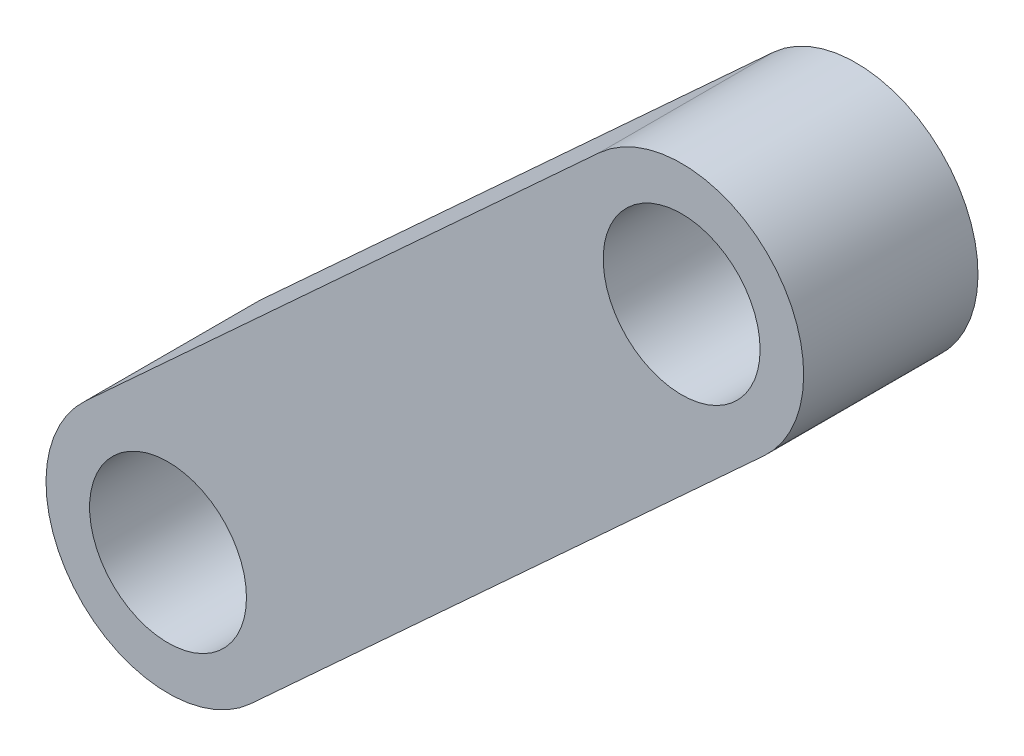
SolidWorks part; units mm, degrees
ref_plane "Front Plane" through (0, 0, 0) normal (0, 0, 1) x (1, 0, 0)
ref_plane "Top Plane" through (0, 0, 0) normal (0, 1, 0) x (1, 0, 0)
ref_plane "Right Plane" through (0, 0, 0) normal (1, 0, 0) x (0, 0, -1)
sketch "Sketch1" plane through (0, 0, 0) normal (0, 0, 1) x (1, 0, 0)
  line L0 (0, 0) -> (294.6187, 270.5547) construction
  line L1 (-47.3471, 51.5583) -> (247.2716, 322.1129)
  line L2 (47.3471, -51.5583) -> (341.9658, 218.9964)
  arc A0 (-47.3471, 51.5583) -> (47.3471, -51.5583) centre (0, 0) ccw
  arc A1 (341.9658, 218.9964) -> (247.2716, 322.1129) centre (294.6187, 270.5547) ccw
  circle A2 centre (0, 0) radius 45
  circle A3 centre (294.6187, 270.5547) radius 45
  point P3 (147.3093, 135.2773)
  dimension "D1" = 90
  dimension "D2" = 90
  dimension "D4" = 70
  dimension "D3" = 400
extrude "Boss-Extrude1" add sketch "Sketch1" along normal blind 100
